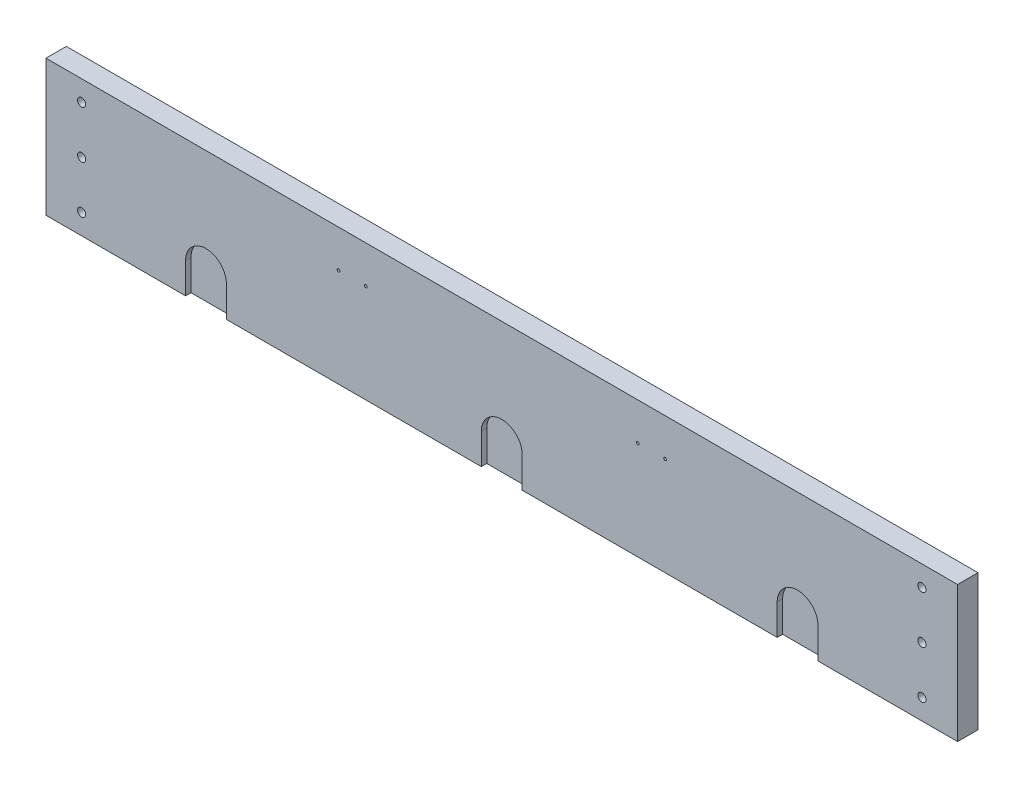
SolidWorks part; units mm, degrees
ref_plane "Front Plane" through (0, 0, 0) normal (0, 0, 1) x (1, 0, 0)
ref_plane "Top Plane" through (0, 0, 0) normal (0, 1, 0) x (1, 0, 0)
ref_plane "Right Plane" through (0, 0, 0) normal (1, 0, 0) x (0, 0, -1)
sketch "Sketch1" plane through (0, 0, 0) normal (0, 1, 0) x (1, 0, 0)
  line L0 (0, 0) -> (812.8, 0)
  line L4 (0, 0) -> (-19.05, 0)
  line L7 (812.8, 0) -> (831.85, 0)
  line L13 (812.8, 0) -> (812.8, -19.05)
  line L14 (812.8, -19.05) -> (0, -19.05)
  line L15 (0, -19.05) -> (0, 0)
  line L18 (-19.05, 0) -> (-19.05, -19.05)
  line L19 (-19.05, -19.05) -> (0, -19.05)
  line L20 (831.85, 0) -> (831.85, -19.05)
  line L21 (831.85, -19.05) -> (812.8, -19.05)
  dimension "D3" = 19.05
  dimension "D6" = 19.05
extrude "Boss-Extrude2" add sketch "Sketch1" along normal blind 127 contours L15 L14 L13 L0 | L21 L20 L7 L13 | L18 L19 L15 L4
sketch "Sketch2" plane through (0, 0, 0) normal (0, 0, -1) x (-1, 0, 0)
  line L0 (19.05, 127) -> (-831.85, 127) construction
  line L1 (-831.85, 127) -> (-831.85, 0) construction
  line L3 (-406.4, 127) -> (-406.4, 0)
  line L4 (19.05, 0) -> (-831.85, 0) construction
  circle A0 centre (-798.576, 107.95) radius 3.81
  circle A1 centre (-798.576, 63.5) radius 3.81
  circle A2 centre (-798.576, 19.05) radius 3.81
  circle A3 centre (-14.224, 19.05) radius 3.81
  circle A4 centre (-14.224, 63.5) radius 3.81
  circle A5 centre (-14.224, 107.95) radius 3.81
  dimension "D2" = 7.62
  dimension "D5" = 7.62
  dimension "D8" = 7.62
  dimension "D1" = 19.05
  dimension "D3" = 33.274
  dimension "D4" = 33.274
  dimension "D6" = 44.45
  dimension "D7" = 44.45
  dimension "D9" = 33.274
extrude "Cut-Extrude1" cut sketch "Sketch2" against normal blind 19.05 contours A5 | A4 | A3 | A2 | A0 | A1
sketch "Sketch3" plane through (0, 0, 0) normal (0, 0, -1) x (-1, 0, 0)
  line L0 (-831.85, 127) -> (-831.85, 0) construction
  line L1 (19.05, 127) -> (19.05, 0) construction
  line L2 (19.05, 0) -> (-831.85, 0) construction
  line L3 (-701.548, 28.702) -> (-701.548, 0)
  line L4 (-663.448, 28.702) -> (-663.448, 0)
  line L5 (-387.35, 28.702) -> (-387.35, 0)
  line L6 (-425.45, 28.702) -> (-425.45, 0)
  line L7 (-111.252, 28.702) -> (-111.252, 0)
  line L8 (-149.352, 28.702) -> (-149.352, 0)
  circle A0 centre (-682.498, 28.702) radius 19.05
  circle A1 centre (-406.4, 28.702) radius 19.05
  circle A2 centre (-130.302, 28.702) radius 19.05
  line M7 (-831.85, 0) -> (19.05, 0)
  dimension "D1" = 38.1
  dimension "D2" = 38.1
  dimension "D3" = 38.1
  dimension "D4" = 149.352
  dimension "D5" = 276.098
  dimension "D6" = 276.098
  dimension "D7" = 149.352
  dimension "D8" = 28.702
  dimension "D9" = 28.702
extrude "Cut-Extrude2" cut sketch "Sketch3" against normal blind 19.05 contours A0 L3 L4 M7 | A0 | A1 | A1 L6 L5 M7 | A2 L8 L7 M7 | A2
sketch "Sketch4" plane through (0, 0, 0) normal (0, 0, -1) x (-1, 0, 0)
  line L0 (-111.252, 28.702) -> (-111.252, 0)
  line L1 (-149.352, 28.702) -> (-149.352, 0)
  line L2 (-425.45, 28.702) -> (-425.45, 0)
  line L3 (-387.35, 28.702) -> (-387.35, 0)
  line L4 (-663.448, 28.702) -> (-663.448, 0)
  line L5 (-701.548, 28.702) -> (-701.548, 0)
  line L6 (-701.548, 0) -> (-663.448, 0)
  line L7 (-425.45, 0) -> (-387.35, 0)
  line L8 (-149.352, 0) -> (-111.252, 0)
  circle A0 centre (-682.498, 28.702) radius 19.05
  circle A1 centre (-406.4, 28.702) radius 19.05
  circle A2 centre (-130.302, 28.702) radius 19.05
  arc M12 (-701.548, 28.702) -> (-663.448, 28.702) centre (-682.498, 28.702) cw
  line M13 (-663.448, 28.702) -> (-663.448, 0)
  line M15 (-425.45, 0) -> (-425.45, 28.702)
  arc M16 (-425.45, 28.702) -> (-387.35, 28.702) centre (-406.4, 28.702) cw
  line M17 (-387.35, 28.702) -> (-387.35, 0)
  line M19 (-149.352, 0) -> (-149.352, 28.702)
  arc M20 (-149.352, 28.702) -> (-111.252, 28.702) centre (-130.302, 28.702) cw
  line M21 (-111.252, 28.702) -> (-111.252, 0)
  line M27 (-701.548, 0) -> (-701.548, 28.702)
extrude "Boss-Extrude3" add sketch "Sketch4" against normal blind 13.97 contours A1 L7 M15 M17 | A1 M16 | A2 L8 M19 M21 | A2 M20 | A0 L6 M27 M13 | A0 M12
sketch "Sketch5" plane through (0, 0, 19.05) normal (0, 0, 1) x (1, 0, 0)
  line L0 (406.4, 127) -> (406.4, 0)
  line L1 (831.85, 127) -> (-19.05, 127) construction
  line L2 (-19.05, 127) -> (-19.05, 0) construction
  circle A0 centre (254, 91.948) radius 1.27
  circle A1 centre (279.4, 91.948) radius 1.27
  circle A2 centre (533.4, 91.948) radius 1.27
  circle A3 centre (558.8, 91.948) radius 1.27
  dimension "D1" = 2.54
  dimension "D2" = 2.54
  dimension "D4" = 35.052
  dimension "D5" = 273.05
  dimension "D6" = 298.45
  dimension "D3" = 35.052
extrude "Cut-Extrude3" cut sketch "Sketch5" against normal blind 19.05 contours A0 | A1 | A2 | A3
